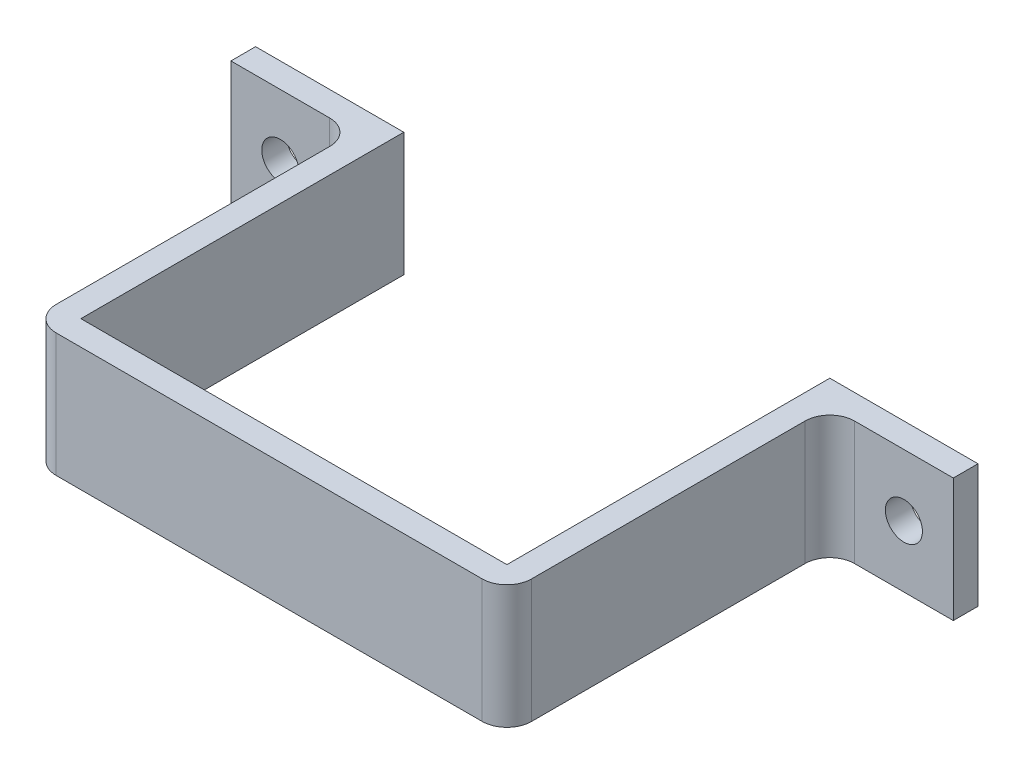
SolidWorks part; units mm, degrees
ref_plane "Front Plane" through (0, 0, 0) normal (0, 0, 1) x (1, 0, 0)
ref_plane "Top Plane" through (0, 0, 0) normal (0, 1, 0) x (1, 0, 0)
ref_plane "Right Plane" through (0, 0, 0) normal (1, 0, 0) x (0, 0, -1)
sketch "Sketch1" plane through (0, 0, 0) normal (0, 0, 1) x (1, 0, 0)
  line L0 (-17, -17.5) -> (-17, 17.5) construction
  line L1 (-17.25, 10.5451) -> (17.25, 10.5451)
  line L2 (-17.25, 10.5451) -> (-17.25, 0.5451)
  line L3 (-17.25, 0.5451) -> (17.25, 0.5451)
  line L4 (15, -17.5) -> (15, 17.5)
  line L5 (15, 17.5) -> (-15, 17.5)
  line L6 (-15, 17.5) -> (-15, -17.5)
  line L7 (-15, -17.5) -> (15, -17.5)
  line L8 (15, -17.5) -> (15, 17.5)
  line L9 (15, 17.5) -> (-15, 17.5) construction
  line L10 (-15, 17.5) -> (-15, -17.5)
  line L11 (-15, -17.5) -> (15, -17.5)
  line L12 (17.25, 10.5451) -> (17.25, 0.5451)
  line L13 (17, 17.5) -> (17, -17.5) construction
  dimension "D2" = 0.25
  dimension "D3" = 0.25
  dimension "D4" = 10
  dimension "D5" = 6.9549
extrude "Boss-Extrude1" add sketch "Sketch1" along normal blind 2 from offset 0.15 contours L1 L10 L3 L8 | L12 L1 L8 L3 | L10 L1 L2 L3
sketch "Sketch2" plane through (0, 0, 2.15) normal (0, 0, 1) x (1, 0, 0)
  line L1 (-17.25, 10.5451) -> (-19.25, 10.5451)
  line L2 (-17.25, 10.5451) -> (-17.25, 0.5451)
  line L3 (-17.25, 0.5451) -> (-19.25, 0.5451)
  line L4 (17.25, 10.5451) -> (-17.25, 10.5451)
  line L5 (-17.25, 10.5451) -> (-17.25, 0.5451)
  line L6 (-17.25, 0.5451) -> (17.25, 0.5451)
  line L7 (17.25, 0.5451) -> (17.25, 10.5451)
  line L8 (17.25, 10.5451) -> (-17.25, 10.5451)
  line L9 (-17.25, 10.5451) -> (-17.25, 0.5451)
  line L10 (-17.25, 0.5451) -> (17.25, 0.5451)
  line L11 (17.25, 0.5451) -> (17.25, 10.5451)
  line L12 (-19.25, 10.5451) -> (-19.25, 0.5451)
  line L13 (17.25, 10.5451) -> (19.25, 10.5451)
  line L14 (17.25, 10.5451) -> (17.25, 0.5451)
  line L15 (17.25, 0.5451) -> (19.25, 0.5451)
  line L16 (19.25, 10.5451) -> (19.25, 0.5451)
  line M14 (-17.25, 10.5451) -> (-17.25, 0.5451)
  line M16 (17.25, 0.5451) -> (17.25, 10.5451)
  dimension "D2" = 2
extrude "Boss-Extrude2" add sketch "Sketch2" against normal up to surface (28.15 mm away) contours L16 L13 L15 M16 | L1 L12 L3 M14
sketch "Sketch3" plane through (-19.25, 0, 0) normal (-1, 0, 0) x (0, 0, 1)
  line L0 (-26, 0.5451) -> (2.15, 0.5451) construction
  line L1 (-26, 10.5451) -> (-24, 10.5451)
  line L2 (-26, 10.5451) -> (-26, 0.5451)
  line L3 (-26, 0.5451) -> (-24, 0.5451)
  line L4 (-24, 10.5451) -> (-24, 0.5451)
  dimension "D1" = 2
extrude "Boss-Extrude3" add sketch "Sketch3" along normal blind 10
mirror "Mirror1" about plane through (0, 0, 0) normal (1, 0, 0) of "Boss-Extrude3"
fillet "Fillet1" radius 2 4 edges at (-19.25, 5.5451, -24) (-19.25, 5.5451, 2.15) (19.25, 5.5451, -24) (19.25, 5.5451, 2.15)
sketch "Sketch4" plane through (0, 0, -24) normal (0, 0, 1) x (1, 0, 0)
  line L0 (-20.25, 5.5451) -> (-25.25, 5.5451)
  line L4 (-29.25, 0.5451) -> (-21.25, 0.5451)
  line L5 (-21.25, 0.5451) -> (-21.25, 10.5451)
  line L6 (-21.25, 10.5451) -> (-29.25, 10.5451)
  line L7 (-29.25, 10.5451) -> (-29.25, 0.5451)
  line L8 (-29.25, 0.5451) -> (-21.25, 0.5451)
  line L10 (-21.25, 10.5451) -> (-29.25, 10.5451)
  line L11 (-29.25, 10.5451) -> (-29.25, 0.5451)
  line L14 (-21.25, 0.5451) -> (-21.25, 10.5451)
  circle A0 centre (-25.25, 5.5451) radius 1.5
  point P10 (-25.25, 0.5451)
  dimension "D2" = 3
extrude "Cut-Extrude1" cut sketch "Sketch4" against normal up to surface (2 mm away) and the other way through all up to face at (-23.25, 5.5451, -26)
mirror "Mirror2" about plane through (0, 0, 0) normal (1, 0, 0) of "Cut-Extrude1"
equation "\"C\"=0.25"
equation "\"D2@Sketch1\"=\"C\""
equation "\"D3@Sketch1\"=\"C\""
equation "\"W\"=12.2844"
equation "\"T\"=2"
equation "\"D1@Boss-Extrude1\"=\"T\""
equation "\"D2@Sketch2\"=\"T\""
equation "\"D1@Sketch3\"=\"T\""
equation "\"FL\"=10"
equation "\"D1@Boss-Extrude3\"=\"FL\""
equation "\"F\"=2"
equation "\"D1@Fillet1\"=\"F\""
equation "\"SCREWD\"=3"
equation "\"D2@Sketch4\"=\"SCREWD\""
